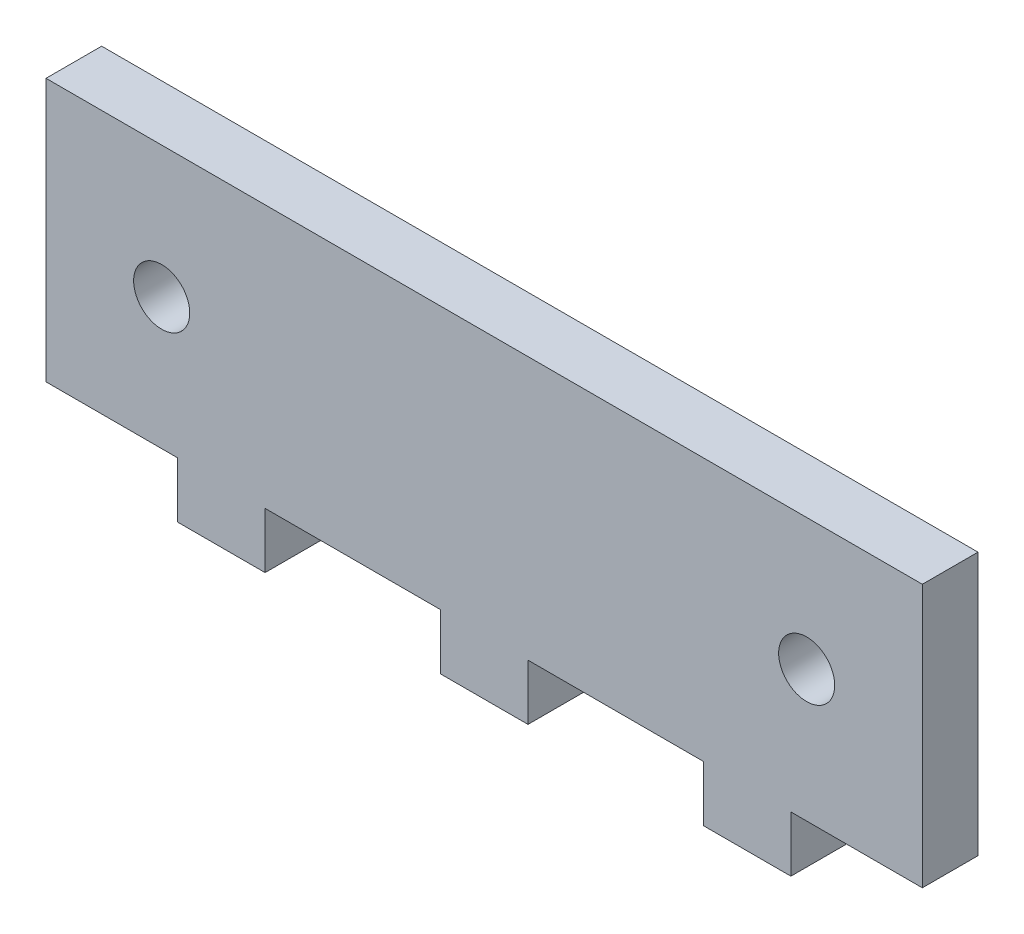
SolidWorks part; units mm, degrees
ref_plane "Front Plane" through (0, 0, 0) normal (0, 0, 1) x (1, 0, 0)
ref_plane "Top Plane" through (0, 0, 0) normal (0, 1, 0) x (1, 0, 0)
ref_plane "Right Plane" through (0, 0, 0) normal (1, 0, 0) x (0, 0, -1)
sketch "Sketch1" plane through (0, 0, 0) normal (0, 0, 1) x (1, 0, 0)
  line L0 (0, 0) -> (0, -10.675) construction
  line L1 (25, 7.5) -> (-25, 7.5)
  line L2 (25, 7.5) -> (25, -7.5)
  line L3 (25, -7.5) -> (17.5, -7.5)
  line L4 (-25, 7.5) -> (-25, -7.5)
  line L5 (25, 7.5) -> (-25, -7.5) construction
  line L6 (25, -7.5) -> (-25, 7.5) construction
  line L8 (-17.5, -7.5) -> (-17.5, -10.675)
  line L9 (-17.5, -10.675) -> (-12.5, -10.675)
  line L10 (-12.5, -7.5) -> (-12.5, -10.675)
  line L12 (-2.5, -7.5) -> (-2.5, -10.675)
  line L13 (-2.5, -10.675) -> (2.5, -10.675)
  line L14 (2.5, -7.5) -> (2.5, -10.675)
  line L16 (12.5, -7.5) -> (12.5, -10.675)
  line L17 (12.5, -10.675) -> (17.5, -10.675)
  line L18 (17.5, -7.5) -> (17.5, -10.675)
  line L19 (-17.5, -7.5) -> (-25, -7.5)
  line L20 (-2.5, -7.5) -> (-12.5, -7.5)
  line L21 (12.5, -7.5) -> (2.5, -7.5)
  point P0 (0, 0)
  point P20 (0, -10.675)
  dimension "D1" = 15
  dimension "D2" = 50
  dimension "D3" = 5
  dimension "D4" = 5
  dimension "D5" = 5
  dimension "D6" = 10
  dimension "D7" = 10
  dimension "D8" = 3.175
  dimension "D9" = 3.175
  dimension "D10" = 3.175
extrude "Boss-Extrude1" add sketch "Sketch1" along normal blind 3.175
sketch "Sketch2" plane through (0, 0, 3.175) normal (0, 0, 1) x (1, 0, 0)
  line L1 (-25, 0) -> (25, 0) construction
  line L2 (-25, 7.5) -> (-25, -7.5) construction
  line L3 (25, -7.5) -> (25, 7.5) construction
  circle A0 centre (-18.4, 0) radius 1.6
  circle A1 centre (18.4, 0) radius 1.6
  dimension "D1" = 3.2
  dimension "D2" = 3.2
  dimension "D3" = 36.8
  dimension "D4" = 18.4
extrude "Cut-Extrude1" cut sketch "Sketch2" against normal blind 3.175
